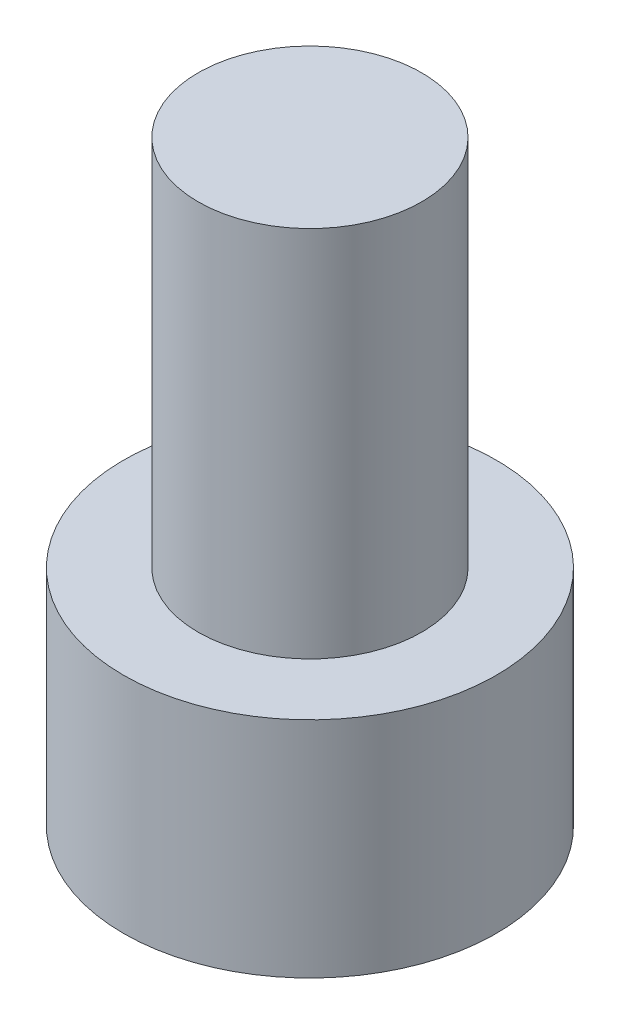
SolidWorks part; units mm, degrees
ref_plane "前视基准面" through (0, 0, 0) normal (0, 0, 1) x (1, 0, 0)
ref_plane "上视基准面" through (0, 0, 0) normal (0, 1, 0) x (1, 0, 0)
ref_plane "右视基准面" through (0, 0, 0) normal (1, 0, 0) x (0, 0, -1)
sketch "草图1" plane through (0, 0, 0) normal (0, 1, 0) x (1, 0, 0)
  circle A0 centre (0, 0) radius 2.5
  dimension "D1" = 5
extrude "凸台-拉伸1" add sketch "草图1" along normal blind 3
sketch "草图2" plane through (0, 3, 0) normal (0, 1, 0) x (1, 0, 0)
  circle A0 centre (0, 0) radius 1.5
extrude "凸台-拉伸2" add sketch "草图2" along normal blind 5
sketch "草图3" plane through (0, 0, 0) normal (0, -1, 0) x (1, 0, 0)
  line L1 (1.425, 0) -> (0.7125, 1.2341)
  line L2 (0.7125, 1.2341) -> (-0.7125, 1.2341)
  line L3 (-0.7125, 1.2341) -> (-1.425, 0)
  line L4 (-1.425, 0) -> (-0.7125, -1.2341)
  line L5 (-0.7125, -1.2341) -> (0.7125, -1.2341)
  line L6 (0.7125, -1.2341) -> (1.425, 0)
  circle A0 centre (0, 0) radius 1.2341 construction
extrude "切除-拉伸1" cut sketch "草图3" against normal blind 1.65
